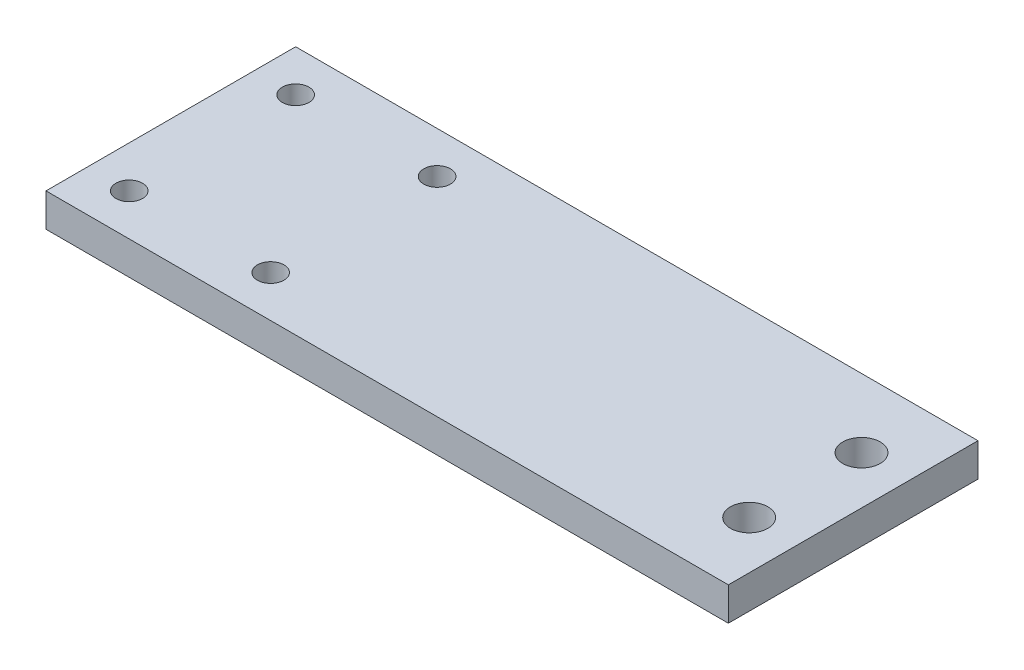
SolidWorks part; units mm, degrees
ref_plane "前视基准面" through (0, 0, 0) normal (0, 0, 1) x (1, 0, 0)
ref_plane "上视基准面" through (0, 0, 0) normal (0, 1, 0) x (1, 0, 0)
ref_plane "右视基准面" through (0, 0, 0) normal (1, 0, 0) x (0, 0, -1)
sketch "草图1" plane through (0, 0, 0) normal (0, 1, 0) x (1, 0, 0)
  line L0 (-42, 10) -> (40, 10) construction
  line L2 (40, -5) -> (40, 25)
  line L4 (-42, -5) -> (-42, 25)
  line L5 (-1, 30) -> (-1, -10) construction
  line L6 (-42, 25) -> (40, 25)
  line L7 (-42, -5) -> (40, -5)
  circle A0 centre (-20, 20) radius 1.6
  circle A1 centre (-37, 20) radius 1.6
  circle A2 centre (-20, 0) radius 1.6
  circle A3 centre (-37, 0) radius 1.6
  circle A8 centre (34.25, 16.75) radius 2.25
  circle A9 centre (34.25, 3.25) radius 2.25
  point P0 (0, 0)
  dimension "D3" = 5
  dimension "D4" = 22
  dimension "D7" = 4.5
  dimension "D5" = 10
  dimension "D6" = 10
  dimension "D8" = 5.75
  dimension "D9" = 6.75
  dimension "D10" = 15
extrude "凸台-拉伸1" add sketch "草图1" along normal blind 4
